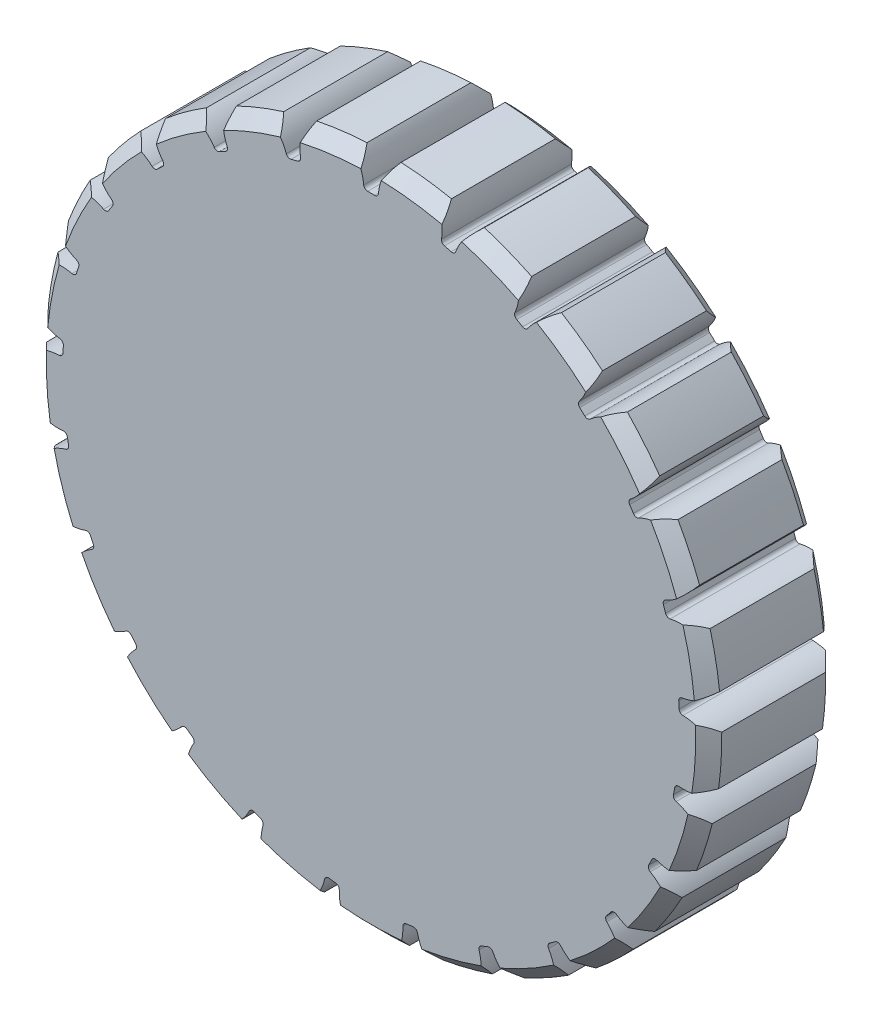
SolidWorks part; units mm, degrees
material "AISI 1020"
ref_plane "Plan de face" through (0, 0, 0) normal (0, 0, 1) x (1, 0, 0)
ref_plane "Plan de dessus" through (0, 0, 0) normal (0, 1, 0) x (1, 0, 0)
ref_plane "Plan de droite" through (0, 0, 0) normal (1, 0, 0) x (0, 0, -1)
sketch "Sketch1" plane through (0, 0, 0) normal (0, 0, 1) x (1, 0, 0)
  circle A1 centre (0, 0) radius 52
  dimension "addendumD" = 104
extrude "Boss-Extrude1" add sketch "Sketch1" along normal mid plane 20
sketch "Sketch3" plane through (0, 0, 10) normal (0, 0, 1) x (1, 0, 0)
  line L0 (0, 0) -> (0, 52) construction
  line L1 (0, 0) -> (6.5173, 51.59) construction
  line L2 (0, 0) -> (3.2651, 51.8974) construction
  line L3 (0, 0) -> (-1.102, 47.4872) construction
  line L4 (-1.5705, 49.9753) -> (1.5705, 49.9753) construction
  line L5 (1.5705, 49.9753) -> (4.7054, 49.7781) construction
  line L6 (-2.2891, 51.9496) -> (0, 45.6603) construction
  circle A0 centre (0, 0) radius 50 construction
  circle A1 centre (0, 0) radius 48 construction
  circle A2 centre (0, 0) radius 52 construction
  arc A4 (-2.6201, 51.934) -> (-1.102, 47.4872) centre (-8.904, 47.3062) cw
  arc A5 (2.6201, 51.934) -> (1.102, 47.4872) centre (8.904, 47.3062) ccw
  arc A6 (1.102, 47.4872) -> (-1.102, 47.4872) centre (0, 0) ccw
  arc A7 (2.6201, 51.934) -> (-2.6201, 51.934) centre (0, 0) ccw
  dimension "PitchD" = 100
  dimension "Addendum&dedendum" = 4
  dimension "ToothAngle" = 7.2
  dimension "PressureAngle" = 20
  dimension "Dedendum" = 2.5
extrude "Cut-Extrude2" cut sketch "Sketch3" against normal up to next (20 mm away)
fillet "Fillet2" radius 0.6 2 edges at (1.102, 47.4872, 0) (-1.102, 47.4872, 0)
chamfer "Chamfer1" distance 2 angle 45 2 edges at (0, -52, -10) (0, -52, 10)
pattern_circular "CirPattern1" count 25 over 360 about axis through (0, 0, 0) along (0, 0, 1) of "Fillet2", "Cut-Extrude2"
equation "\"Module\"= 2mm"
equation "\"Number of teeth\"= 25"
equation "\"Pressre angle\"= 20mm"
equation "\"addendumD@Sketch1\" = ( \"Module\" * 50 )  + 2 * \"Module\""
equation "\"PitchD@Sketch3\" = \"Module\" * 50"
equation "\"ToothAngle@Sketch3\" = 360 /50"
equation "\"PressureAngle@Sketch3\"=\"Pressre angle\""
equation "\"FilletR@Fillet2\"=0.3 * \"Module\""
equation "\"TeethNo@CirPattern1\"=\"Number of teeth\""
equation "\"ChamferDis@Chamfer1\"=\"Module\""
equation "\"Addendum&dedendum@Sketch3\"=2 * \"Module\""
equation "\"Dedendum@Sketch3\"=( 1.25 * \"Module\" )"
